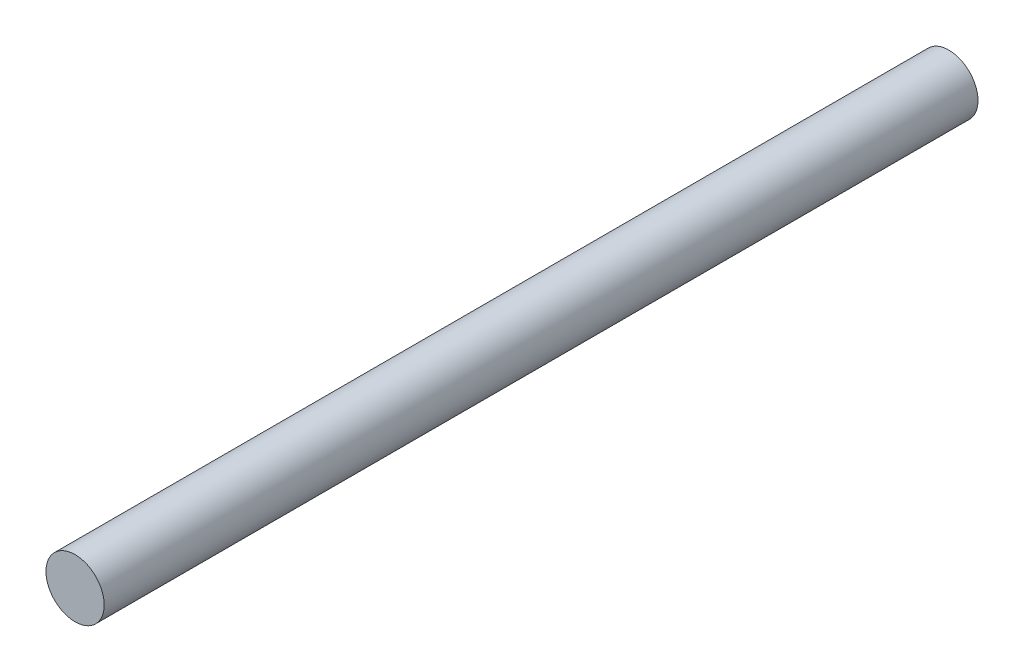
SolidWorks part; units mm, degrees
ref_plane "Front Plane" through (0, 0, 0) normal (0, 0, 1) x (1, 0, 0)
ref_plane "Top Plane" through (0, 0, 0) normal (0, 1, 0) x (1, 0, 0)
ref_plane "Right Plane" through (0, 0, 0) normal (1, 0, 0) x (0, 0, -1)
sketch "Sketch1" plane through (0, 0, 0) normal (0, 0, 1) x (1, 0, 0)
  circle A0 centre (0, 0) radius 1.5
  dimension "D1" = 3
extrude "Boss-Extrude1" add sketch "Sketch1" along normal blind 45
